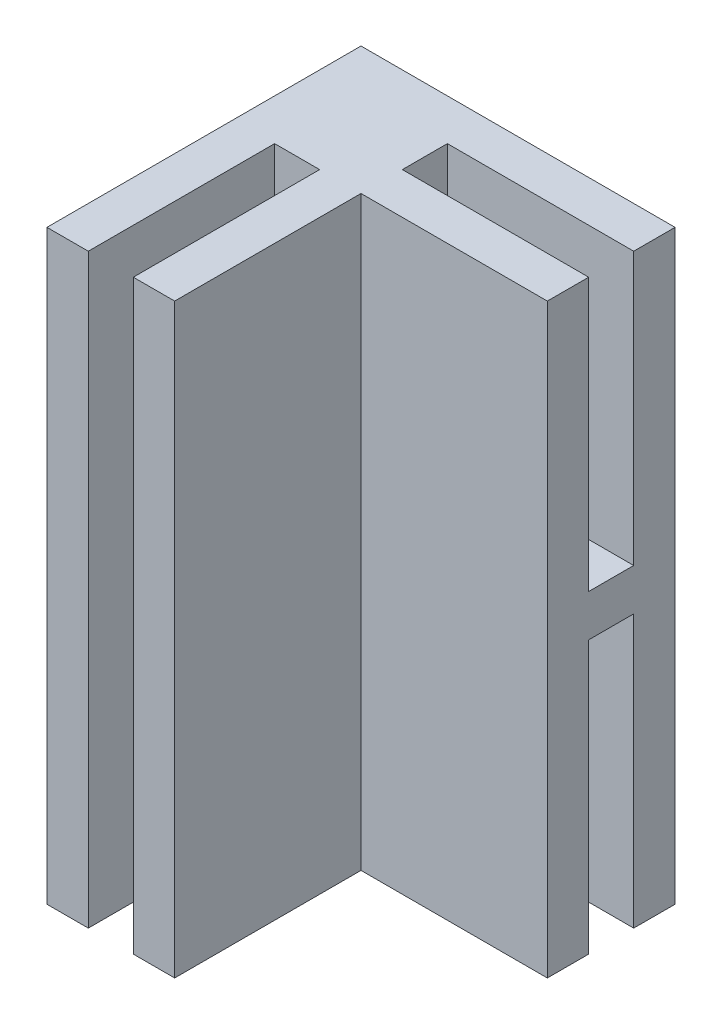
SolidWorks part; units mm, degrees
ref_plane "Plan de face" through (0, 0, 0) normal (0, 0, 1) x (1, 0, 0)
ref_plane "Plan de dessus" through (0, 0, 0) normal (0, 1, 0) x (1, 0, 0)
ref_plane "Plan de droite" through (0, 0, 0) normal (1, 0, 0) x (0, 0, -1)
sketch "Esquisse1" plane through (0, 0, 0) normal (0, 1, 0) x (1, 0, 0)
  line L1 (-11.3793, 9.3842) -> (18.6207, 9.3842)
  line L2 (-11.3793, 9.3842) -> (-11.3793, -20.6158)
  line L3 (-11.3793, -20.6158) -> (18.6207, -20.6158)
  line L4 (18.6207, 9.3842) -> (18.6207, -20.6158)
  dimension "D1" = 30
  dimension "D2" = 30
extrude "Boss.-Extru.1" add sketch "Esquisse1" along normal blind 56
sketch "Esquisse2" plane through (0, 0, 0) normal (0, -1, 0) x (1, 0, 0)
  line L0 (18.6207, 20.6158) -> (18.6207, -9.3842) construction
  line L5 (18.6207, -5.4342) -> (0.8207, -5.4342)
  line L6 (18.6207, -5.4342) -> (18.6207, -1.1342)
  line L7 (18.6207, -1.1342) -> (0.8207, -1.1342)
  line L8 (0.8207, -5.4342) -> (0.8207, -1.1342)
  line L15 (18.6207, -9.3842) -> (-11.3793, -9.3842) construction
  dimension "D1" = 4.3
  dimension "D2" = 3.95
  dimension "D3" = 17.8
extrude "Enlèv. mat.-Extru.1" cut sketch "Esquisse2" against normal blind 26
sketch "Esquisse3" plane through (0, 0, 0) normal (0, -1, 0) x (1, 0, 0)
  line L8 (-11.3793, 20.6158) -> (18.6207, 20.6158) construction
  line L9 (-3.1293, 20.6158) -> (-7.4293, 20.6158)
  line L10 (-3.1293, 20.6158) -> (-3.1293, 2.8158)
  line L11 (-3.1293, 2.8158) -> (-7.4293, 2.8158)
  line L12 (-7.4293, 20.6158) -> (-7.4293, 2.8158)
  line L14 (-11.3793, -9.3842) -> (-11.3793, 20.6158) construction
  line L16 (18.6207, 20.6158) -> (0.8207, 20.6158)
  line L17 (18.6207, 20.6158) -> (18.6207, 2.8158)
  line L18 (18.6207, 2.8158) -> (0.8207, 2.8158)
  line L19 (0.8207, 20.6158) -> (0.8207, 2.8158)
  dimension "D1" = 4.3
  dimension "D2" = 17.8
  dimension "D3" = 3.95
  dimension "D4" = 3.95
extrude "Enlèv. mat.-Extru.2" cut sketch "Esquisse3" against normal through all
sketch "Esquisse4" plane through (0, 56, 0) normal (0, 1, 0) x (1, 0, 0)
  line L0 (18.6207, -2.8158) -> (18.6207, 9.3842) construction
  line L1 (18.6207, 5.4342) -> (0.8207, 5.4342)
  line L2 (18.6207, 5.4342) -> (18.6207, 1.1342)
  line L3 (18.6207, 1.1342) -> (0.8207, 1.1342)
  line L4 (0.8207, 5.4342) -> (0.8207, 1.1342)
  line L5 (18.6207, 9.3842) -> (-11.3793, 9.3842) construction
  dimension "D1" = 4.3
  dimension "D2" = 3.95
  dimension "D3" = 17.8
extrude "Enlèv. mat.-Extru.3" cut sketch "Esquisse4" against normal blind 26
